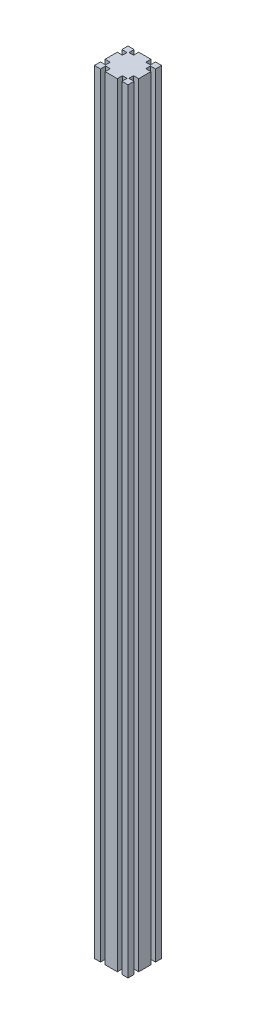
SolidWorks part; units mm, degrees
ref_plane "前视基准面" through (0, 0, 0) normal (0, 0, 1) x (1, 0, 0)
ref_plane "上视基准面" through (0, 0, 0) normal (0, 1, 0) x (1, 0, 0)
ref_plane "右视基准面" through (0, 0, 0) normal (1, 0, 0) x (0, 0, -1)
sketch "草图1" plane through (0, 0, 0) normal (0, 1, 0) x (1, 0, 0)
  line L0 (0, 60) -> (0, 49.1)
  line L1 (0, 0) -> (60, 0)
  line L2 (0, 0) -> (0, 60)
  line L3 (0, 60) -> (60, 60)
  line L4 (60, 0) -> (60, 60)
  line L5 (0, 0) -> (60, 60) construction
  line L6 (0, 60) -> (60, 0) construction
  line L7 (0, 49.1) -> (9.2, 49.1)
  line L8 (9.2, 49.1) -> (9.2, 40.9)
  line L9 (9.2, 40.9) -> (0, 40.9)
  line L10 (0, 30) -> (30, 30)
  line L11 (30, 30) -> (30, 60)
  line L12 (60, 49.1) -> (50.8, 49.1)
  line L13 (50.8, 49.1) -> (50.8, 40.9)
  line L14 (50.8, 40.9) -> (60, 40.9)
  line L15 (10.9, 0) -> (10.9, 9.2)
  line L16 (10.9, 9.2) -> (19.1, 9.2)
  line L17 (19.1, 9.2) -> (19.1, 0)
  line L18 (10.9, 50.8) -> (19.1, 50.8)
  line L19 (10.9, 60) -> (10.9, 50.8)
  line L20 (19.1, 50.8) -> (19.1, 60)
  line L21 (9.2, 19.1) -> (0, 19.1)
  line L22 (9.2, 10.9) -> (9.2, 19.1)
  line L23 (0, 10.9) -> (9.2, 10.9)
  line L24 (49.1, 60) -> (49.1, 50.8)
  line L25 (49.1, 50.8) -> (40.9, 50.8)
  line L26 (40.9, 50.8) -> (40.9, 60)
  line L27 (50.8, 19.1) -> (60, 19.1)
  line L28 (60, 10.9) -> (50.8, 10.9)
  line L29 (50.8, 10.9) -> (50.8, 19.1)
  line L30 (49.1, 9.2) -> (40.9, 9.2)
  line L31 (49.1, 0) -> (49.1, 9.2)
  line L32 (40.9, 9.2) -> (40.9, 0)
  point P4 (30, 30)
extrude "凸台-拉伸1" add sketch "草图1" along normal blind 1380 contours L20 L18 L19 L3 L0 L7 L8 L9 L2 L10 L11 | L32 L30 L31 L1 L4 L28 L29 L27 L14 L13 L12 L3 L24 L25 L26 L11 L10 L2 L21 L22 L23 L15 L16 L17
